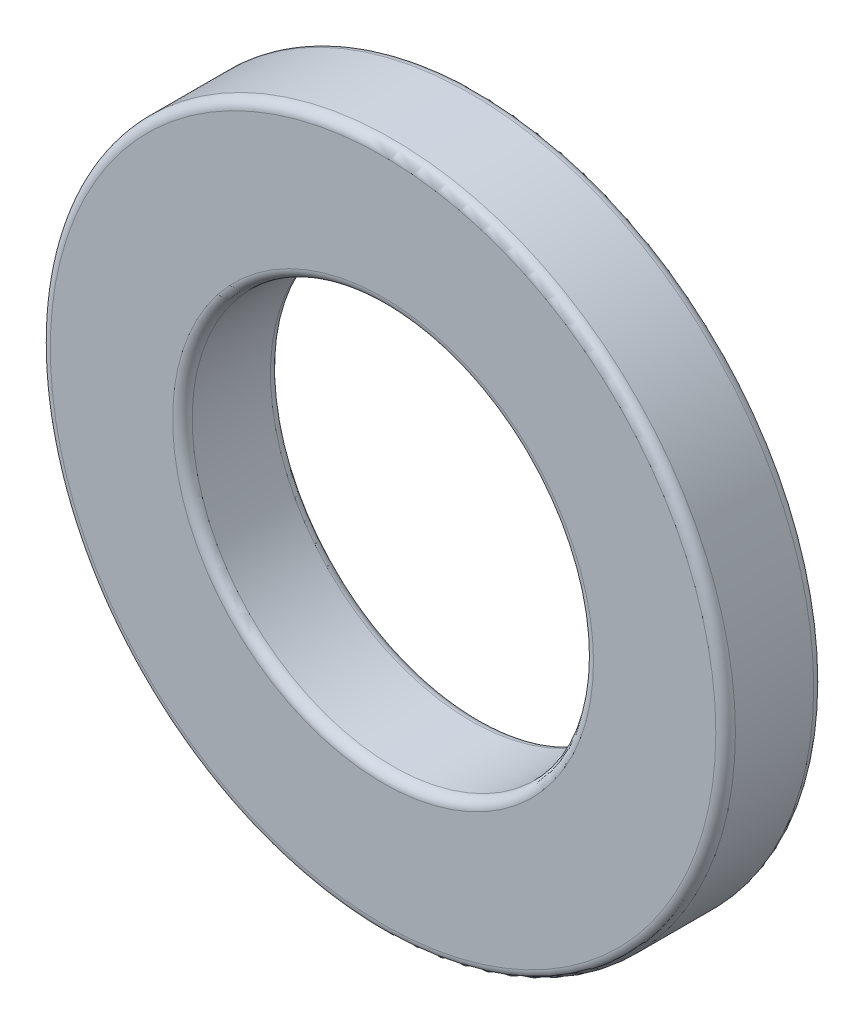
SolidWorks part; units mm, degrees
ref_plane "Спереди" through (0, 0, 0) normal (0, 0, 1) x (1, 0, 0)
ref_plane "Сверху" through (0, 0, 0) normal (0, 1, 0) x (1, 0, 0)
ref_plane "Справа" through (0, 0, 0) normal (1, 0, 0) x (0, 0, -1)
sketch "Эскиз1" plane through (0, 0, 0) normal (0, 0, 1) x (1, 0, 0)
  circle A0 centre (0, 0) radius 4.1
  circle A1 centre (0, 0) radius 7
  dimension "D1" = 8.2
  dimension "D2" = 14
extrude "Бобышка-Вытянуть1" add sketch "Эскиз1" along normal blind 2
fillet "Скругление1" radius 0.2 4 edges at (4.1, 0, 0) (7, 0, 0) (4.1, 0, 2) (7, 0, 2)
